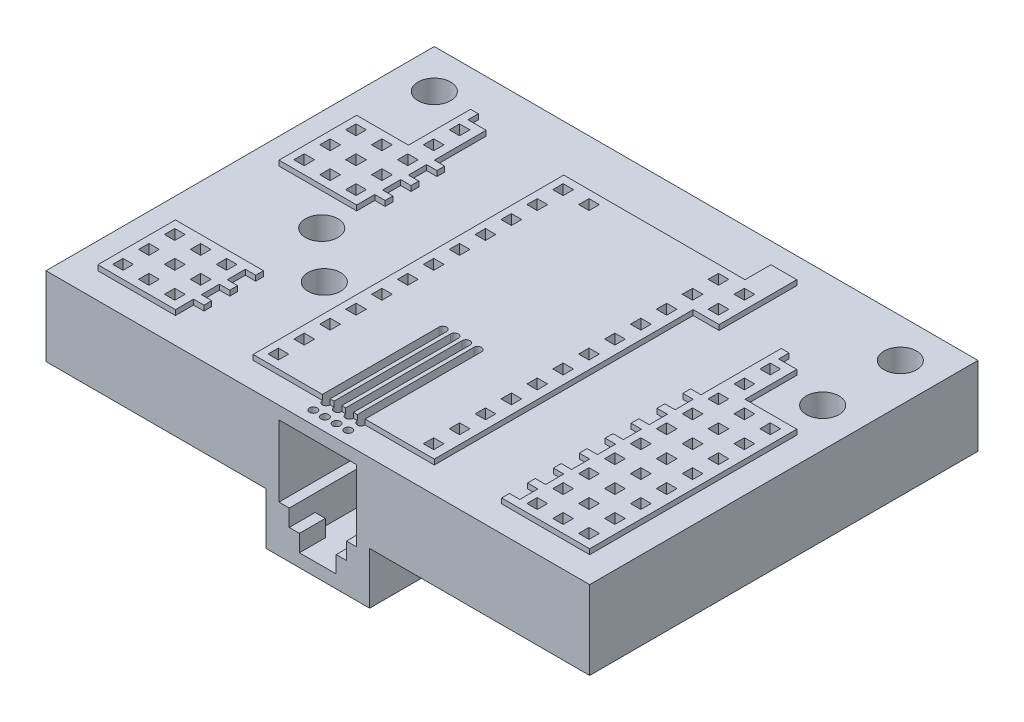
SolidWorks part; units mm, degrees
material "ABS PC"
ref_plane "Front Plane" through (0, 0, 0) normal (0, 0, 1) x (1, 0, 0)
ref_plane "Top Plane" through (0, 0, 0) normal (0, 1, 0) x (1, 0, 0)
ref_plane "Right Plane" through (0, 0, 0) normal (1, 0, 0) x (0, 0, -1)
sketch "Sketch1" plane through (0, 0, 0) normal (0, 1, 0) x (1, 0, 0)
  line L0 (26.67, 19.05) -> (-26.67, -19.05) construction
  line L1 (-26.67, -19.05) -> (26.67, -19.05)
  line L2 (-26.67, -19.05) -> (-26.67, 19.05)
  line L3 (-26.67, 19.05) -> (26.67, 19.05)
  line L4 (26.67, -19.05) -> (26.67, 19.05)
  circle A0 centre (-22.86, 15.24) radius 1.6
  circle A1 centre (22.86, 15.24) radius 1.6
  circle A2 centre (22.86, 7.62) radius 1.6
  circle A3 centre (-16.764, -1.905) radius 1.6
  circle A4 centre (-12.065, -6.35) radius 1.6
  dimension "D3" = 3.2
  dimension "D1" = 38.1
  dimension "D2" = 53.34
  dimension "D4" = 3.81
  dimension "D5" = 3.81
  dimension "D6" = 3.81
  dimension "D7" = 3.81
  dimension "D8" = 3.81
  dimension "D9" = 11.43
  dimension "D10" = 9.906
  dimension "D11" = 14.605
  dimension "D12" = 12.7
  dimension "D13" = 17.145
extrude "breadboard" add sketch "Sketch1" along normal blind 8.2296
sketch "Sketch7" plane through (0, 0, 0) normal (0, -1, 0) x (1, 0, 0)
  line L1 (6.35, 16.256) -> (19.05, 16.256)
  line L2 (6.35, 16.256) -> (6.35, 14.224)
  line L3 (6.35, 14.224) -> (19.05, 14.224)
  line L4 (19.05, 16.256) -> (19.05, 14.224)
  line L6 (-26.67, 19.05) -> (26.67, 19.05) construction
  dimension "D1" = 12.7
  dimension "D2" = 2.032
  dimension "D3" = 2.794
  dimension "D4" = 6.35
extrude "Cut-Extrude5" cut sketch "Sketch7" against normal blind 7.1628
pattern_linear "LPattern4" count 10 spacing 2.54 along (0, 0, -1) count 2 spacing 25.4 along (-1, 0, 0) skipping (3, 1), (4, 1), (5, 1), (6, 1) of "Cut-Extrude5"
sketch "Sketch8" plane through (0, 0, 0) normal (0, -1, 0) x (1, 0, 0)
  line L0 (-26.67, -19.05) -> (-26.67, 19.05) construction
  line L1 (-23.876, 16.51) -> (-21.844, 16.51)
  line L2 (-23.876, 16.51) -> (-23.876, 3.81)
  line L3 (-23.876, 3.81) -> (-21.844, 3.81)
  line L4 (-21.844, 16.51) -> (-21.844, 3.81)
  line L5 (-26.67, 19.05) -> (26.67, 19.05) construction
  dimension "D1" = 12.7
  dimension "D2" = 2.032
  dimension "D3" = 2.794
  dimension "D4" = 2.54
extrude "Cut-Extrude6" cut sketch "Sketch8" against normal blind 7.1628
pattern_linear "LPattern5" count 2 spacing 12.7 along (0, 0, 1) count 2 spacing 2.54 along (1, 0, 0) of "Cut-Extrude6"
sketch "Sketch9" plane through (0, 0, 0) normal (0, -1, 0) x (1, 0, 0)
  line L0 (26.67, 19.05) -> (26.67, -19.05) construction
  line L1 (21.9075, 16.51) -> (23.8125, 16.51)
  line L2 (21.9075, 16.51) -> (21.9075, -3.81)
  line L3 (21.9075, -3.81) -> (23.8125, -3.81)
  line L4 (23.8125, 16.51) -> (23.8125, -3.81)
  line L5 (-26.67, 19.05) -> (26.67, 19.05) construction
  dimension "D1" = 20.32
  dimension "D2" = 1.905
  dimension "D3" = 2.8575
  dimension "D4" = 2.54
extrude "Cut-Extrude7" cut sketch "Sketch9" against normal blind 7.1628
pattern_linear "LPattern6" count 1 spacing 12.7 along (0, 0, -1) count 2 spacing 2.54 along (-1, 0, 0) of "Cut-Extrude7"
sketch "Sketch10" plane through (0, 7.1628, 0) normal (0, -1, 0) x (1, 0, 0)
  line L0 (-23.876, 16.51) -> (-23.876, -8.89) construction
  line L1 (-23.4315, 15.748) -> (-22.4155, 15.748)
  line L2 (-23.4315, 15.748) -> (-23.4315, 14.732)
  line L3 (-23.4315, 14.732) -> (-22.4155, 14.732)
  line L4 (-22.4155, 15.748) -> (-22.4155, 14.732)
  line L5 (-21.844, 16.51) -> (-23.876, 16.51) construction
  dimension "D1" = 1.016
  dimension "D2" = 1.016
  dimension "D3" = 0.4445
  dimension "D4" = 0.762
extrude "Cut-Extrude8" cut sketch "Sketch10" against normal through all
pattern_linear "LPattern8" count 12 spacing 2.54 along (0, 0, -1) count 19 spacing 2.54 along (1, 0, 0) skipping (0, 3), (0, 4), (0, 5), (0, 7), (0, 8), (0, 9), (0, 10), (0, 11), (0, 13), (0, 14), (0, 15), (1, 3), (1, 4), (1, 5), (1, 7), (1, 8), (1, 9), (1, 10), (1, 11), (1, 13), (1, 14), (1, 15), (2, 3), (2, 4), (2, 5), (2, 7), (2, 8), (2, 9), (2, 10), (2, 11), (2, 13), (2, 14), (2, 15), (3, 0), (3, 1), (3, 2), (3, 3), (3, 4), (3, 5), (3, 7), (3, 8), (3, 9), (3, 10), (3, 11), (3, 13), (3, 14), (3, 15), (4, 0), (4, 1), (4, 2), (4, 3), (4, 4), (4, 5), (4, 7), (4, 8), (4, 9), (4, 10), (4, 11), (4, 13), (4, 14), (4, 15), (5, 0), (5, 1), (5, 2), (5, 3), (5, 4), (5, 5), (5, 7), (5, 8), (5, 9), (5, 10), (5, 11), (5, 13), (5, 14), (5, 15), (6, 0), (6, 1), (6, 2), (6, 3), (6, 4), (6, 5), (6, 7), (6, 8), (6, 9), (6, 10), (6, 11), (6, 13), (6, 14), (6, 15), (7, 3), (7, 4), (7, 5), (7, 7), (7, 8), (7, 9), (7, 10), (7, 11), (7, 13), (7, 14), (7, 15), (8, 3), (8, 4), (8, 5), (8, 7), (8, 8), (8, 9), (8, 10), (8, 11), (8, 13), (8, 14), (8, 15), (8, 17), (8, 18), (9, 3), (9, 4), (9, 5), (9, 7), (9, 8), (9, 9), (9, 10), (9, 11), (9, 13), (9, 14), (9, 15), (9, 17), (9, 18), (10, 0), (10, 1), (10, 3), (10, 4), (10, 5), (10, 7), (10, 8), (10, 9), (10, 10), (10, 11), (10, 14), (10, 15), (10, 16), (10, 17), (10, 18), (11, 0), (11, 1), (11, 3), (11, 4), (11, 5), (11, 8), (11, 9), (11, 10), (11, 11), (11, 14), (11, 15), (11, 16), (11, 17), (11, 18) of "Cut-Extrude8"
sketch "Sketch12" plane through (0, 0, 0) normal (0, -1, 0) x (1, 0, 0)
  line L0 (-26.67, -19.05) -> (-26.67, 19.05) construction
  line L1 (-19.05, -9.144) -> (-6.35, -9.144)
  line L2 (-19.05, -9.144) -> (-19.05, -11.176)
  line L3 (-19.05, -11.176) -> (-6.35, -11.176)
  line L4 (-6.35, -9.144) -> (-6.35, -11.176)
  line L5 (26.67, -19.05) -> (-26.67, -19.05) construction
  dimension "D1" = 12.7
  dimension "D2" = 2.032
  dimension "D3" = 7.62
  dimension "D4" = 7.874
extrude "Cut-Extrude9" cut sketch "Sketch12" against normal blind 7.1628
pattern_linear "LPattern9" count 2 spacing 2.54 along (0, 0, -1) of "Cut-Extrude9"
sketch "Sketch47" plane through (0, 0, 0) normal (0, -1, 0) x (1, 0, 0)
  line L0 (-26.67, 19.05) -> (26.67, 19.05) construction
  line L1 (5.08, 6.35) -> (-5.08, 6.35)
  line L2 (5.08, 6.35) -> (5.08, 19.05)
  line L3 (5.08, 19.05) -> (-5.08, 19.05)
  line L4 (-5.08, 6.35) -> (-5.08, 19.05)
  line L5 (26.67, 19.05) -> (26.67, -19.05) construction
  dimension "D1" = 10.16
  dimension "D2" = 12.7
  dimension "D3" = 21.59
extrude "Boss-Extrude5" add sketch "Sketch47" along normal blind 5.08
sketch "Sketch54" plane through (0, 0, 19.05) normal (0, 0, 1) x (1, 0, 0)
  line L1 (-3.81, 6.477) -> (3.81, 6.477)
  line L2 (-3.81, 6.477) -> (-3.81, -0.508)
  line L3 (-1.8034, -3.81) -> (1.8034, -3.81)
  line L4 (3.81, 6.477) -> (3.81, -0.508)
  line L5 (26.67, 8.2296) -> (26.67, 0) construction
  line L7 (-3.81, -0.508) -> (-2.8067, -0.508)
  line L8 (-2.8067, -0.508) -> (-2.8067, -2.159)
  line L9 (-2.8067, -2.159) -> (-1.8034, -2.159)
  line L10 (-1.8034, -2.159) -> (-1.8034, -3.81)
  line L12 (1.8034, -3.81) -> (1.8034, -2.159)
  line L13 (1.8034, -2.159) -> (2.8067, -2.159)
  line L14 (2.8067, -2.159) -> (2.8067, -0.508)
  line L15 (2.8067, -0.508) -> (3.81, -0.508)
  dimension "D1" = 7.62
  dimension "D2" = 22.86
  dimension "D3" = 6.985
  dimension "D5" = 5.6134
  dimension "D6" = 1.0033
  dimension "D7" = 3.6068
  dimension "D8" = 1.0033
  dimension "D9" = 1.651
  dimension "D10" = 1.651
  dimension "D11" = 1.651
  dimension "D12" = 1.651
extrude "Cut-Extrude33" cut sketch "Sketch54" against normal blind 10.9982
sketch "Sketch57" plane through (0, -2.159, 0) normal (0, 1, 0) x (1, 0, 0)
  line L0 (-2.8067, -8.0518) -> (-2.8067, -19.05) construction
  line L1 (2.8067, -6.7818) -> (-2.8067, -6.7818)
  line L2 (2.8067, -6.7818) -> (2.8067, -16.51)
  line L3 (2.8067, -16.51) -> (-2.8067, -16.51)
  line L4 (-2.8067, -6.7818) -> (-2.8067, -16.51)
  dimension "D2" = 9.7282
  dimension "D3" = 5.6134
extrude "Cut-Extrude34" cut sketch "Sketch57" against normal blind 1.651
sketch "Sketch59" plane through (0, 0, 8.0518) normal (0, 0, 1) x (1, 0, 0)
  line L0 (3.81, 6.477) -> (-3.81, 6.477) construction
  line L1 (-2.0955, 6.477) -> (-1.3335, 6.477)
  line L2 (-2.0955, 6.477) -> (-2.0955, 2.413)
  line L3 (-2.0955, 2.413) -> (-1.3335, 2.413)
  line L4 (-1.3335, 6.477) -> (-1.3335, 2.413)
  line L6 (0, -3.81) -> (0, 9.3002) construction
  line L7 (-2.8067, -3.81) -> (2.8067, -3.81) construction
  line L8 (-1.7145, 2.413) -> (-1.7145, 8.2296) construction
  line L9 (-26.67, 8.2296) -> (26.67, 8.2296) construction
  dimension "D1" = 4.064
  dimension "D2" = 0.762
  dimension "D3" = 1.7145
extrude "Cut-Extrude35" cut sketch "Sketch59" against normal blind 5.08
pattern_linear "LPattern25" count 4 spacing 1.143 along (1, 0, 0) of "Cut-Extrude35"
sketch "Sketch62" plane through (0, 8.2296, 0) normal (0, 1, 0) x (1, 0, 0)
  line L1 (-26.67, -19.05) -> (26.67, -19.05) construction
  line L2 (-26.67, 19.05) -> (-26.67, -19.05) construction
  circle A0 centre (-1.7145, -5.08) radius 0.381
  dimension "D1" = 0.762
  dimension "D2" = 24.9555
  dimension "D3" = 13.97
extrude "Cut-Extrude37" cut sketch "Sketch62" against normal blind 7.62
pattern_linear "LPattern27" count 4 spacing 1.143 along (1, 0, 0) count 2 spacing 12.7 along (0, 0, 1) of "Cut-Extrude37"
sketch "Sketch63" plane through (0, 8.2296, 0) normal (0, 1, 0) x (1, 0, 0)
  line L0 (-1.7145, -16.51) -> (-1.7145, -5.08) construction
  line L1 (-2.0955, -16.51) -> (-2.0955, -5.08)
  line L2 (-1.3335, -16.51) -> (-1.3335, -5.08)
  arc A0 (-2.0955, -16.51) -> (-1.3335, -16.51) centre (-1.7145, -16.51) ccw
  arc A1 (-1.3335, -5.08) -> (-2.0955, -5.08) centre (-1.7145, -5.08) ccw
  point P4 (-1.7145, -10.795)
  dimension "D1" = 0.381
extrude "Cut-Extrude38" cut sketch "Sketch63" against normal blind 1.27
pattern_linear "LPattern28" count 4 spacing 1.143 along (1, 0, 0) of "Cut-Extrude38"
sketch "Sketch66" plane through (0, 0, 8.0518) normal (0, 0, 1) x (1, 0, 0)
  line L0 (-2.8067, -0.508) -> (-2.8067, -2.159) construction
  line L1 (-2.8067, -2.2225) -> (2.8067, -2.2225)
  line L2 (-2.8067, -2.2225) -> (-2.8067, 0.9525)
  line L3 (-2.8067, 0.9525) -> (2.8067, 0.9525)
  line L4 (2.8067, -2.2225) -> (2.8067, 0.9525)
  line L6 (-2.8067, -3.81) -> (2.8067, -3.81) construction
  dimension "D1" = 5.6134
  dimension "D2" = 3.175
  dimension "D3" = 1.5875
extrude "Cut-Extrude41" cut sketch "Sketch66" against normal blind 0.508
sketch "Sketch68" plane through (0, 0, 0) normal (0, -1, 0) x (1, 0, 0)
  line L0 (-6.35, -13.716) -> (-6.35, -11.684) construction
  line L1 (-6.0325, -11.684) -> (-0.9525, -11.684)
  line L2 (-6.0325, -11.684) -> (-6.0325, -13.716)
  line L3 (-6.0325, -13.716) -> (-0.9525, -13.716)
  line L4 (-0.9525, -11.684) -> (-0.9525, -13.716)
  line L6 (-6.35, -11.684) -> (-19.05, -11.684) construction
  dimension "D1" = 5.08
  dimension "D2" = 2.032
  dimension "D3" = 0.3175
extrude "Cut-Extrude43" cut sketch "Sketch68" against normal blind 7.1628
sketch "Sketch69" plane through (0, 0, 0) normal (0, -1, 0) x (1, 0, 0)
  line L0 (-19.05, -13.97) -> (-19.05, -8.89)
  line L1 (23.8125, -3.81) -> (23.8125, -5.5419)
  line L2 (19.05, -3.81) -> (23.8125, -3.81)
  line L3 (-19.05, -8.89) -> (-23.876, -8.89)
  line L4 (3.175, 6.096) -> (3.175, -13.97)
  line L5 (3.175, 6.096) -> (-6.35, 6.096)
  line L6 (19.05, 6.096) -> (6.35, 6.096) construction
  line L7 (-6.35, 6.096) -> (-6.35, 4.064)
  line L8 (-23.876, -8.89) -> (-23.876, -13.1922)
  line L9 (-20.9592, -16.51) -> (20.9592, -16.51)
  line L11 (23.8125, -9.6981) -> (23.8125, -13.1619)
  line L12 (-6.35, 4.064) -> (-3.175, 4.064)
  line L13 (-19.05, -13.97) -> (-3.175, -13.97)
  line L15 (19.05, -3.81) -> (19.05, -8.636)
  line L16 (-3.175, -13.97) -> (-3.175, 4.064)
  line L17 (6.35, -8.636) -> (19.05, -8.636) construction
  line L18 (19.05, -8.636) -> (19.05, -6.604) construction
  line L19 (3.175, -13.97) -> (11.43, -13.97)
  line L20 (11.43, -13.97) -> (11.43, -8.636)
  line L21 (6.35, 4.064) -> (19.05, 4.064) construction
  line L22 (11.43, -8.636) -> (19.05, -8.636)
  line L23 (6.35, -6.604) -> (6.35, -8.636) construction
  line L24 (-19.05, -6.604) -> (-19.05, -8.636) construction
  line L25 (0, 0) -> (0, -30.7644) construction
  line L26 (-6.35, 9.144) -> (-6.35, 11.176) construction
  line L31 (26.67, -19.05) -> (-26.67, -19.05) construction
  arc A0 (23.8125, -5.5419) -> (23.8125, -9.6981) centre (22.86, -7.62) ccw
  arc A1 (23.8125, -13.1619) -> (20.9592, -16.51) centre (22.86, -15.24) ccw
  arc A2 (-20.9592, -16.51) -> (-23.876, -13.1922) centre (-22.86, -15.24) ccw
  dimension "D6" = 3.175
  dimension "D1" = 4.572
  dimension "D2" = 2.54
  dimension "D3" = 2.54
  dimension "D4" = 5.08
  dimension "D7" = 3.175
extrude "tracing" cut sketch "Sketch69" against normal blind 1.5748
sketch "Sketch80" plane through (0, 0, 0) normal (0, -1, 0) x (1, 0, 0)
  line L0 (-6.35, 4.064) -> (-3.175, 4.064) construction
  line L1 (-3.81, 6.096) -> (-8.89, 6.096)
  line L2 (-3.81, 6.096) -> (-3.81, 4.064)
  line L3 (-3.81, 4.064) -> (-8.89, 4.064)
  line L4 (-8.89, 6.096) -> (-8.89, 4.064)
  line L5 (-6.35, -3.556) -> (-6.35, -1.524) construction
  line L6 (19.05, 6.096) -> (6.35, 6.096) construction
  line L8 (6.35, 4.064) -> (19.05, 4.064) construction
  dimension "D1" = 5.08
  dimension "D2" = 2.54
extrude "Cut-Extrude52" cut sketch "Sketch80" against normal blind 7.1628
sketch "Sketch77" plane through (0, 0, 0) normal (0, -1, 0) x (1, 0, 0)
  line L0 (-21.844, -8.89) -> (-21.844, 16.51) construction
  line L1 (-23.876, 16.51) -> (-21.844, 16.51)
  line L2 (-23.876, 16.51) -> (-23.876, 17.78)
  line L3 (-23.876, 17.78) -> (-21.844, 17.78)
  line L4 (-21.844, 16.51) -> (-21.844, 17.78)
  dimension "D1" = 1.27
extrude "Cut-Extrude51" cut sketch "Sketch77" against normal blind 1.5748
pattern_linear "LPattern32" count 2 spacing 2.54 along (1, 0, 0) count 2 spacing 26.67 of "Cut-Extrude51"
sketch "Sketch81" plane through (0, 0, 0) normal (0, -1, 0) x (1, 0, 0)
  line L0 (21.2725, -3.81) -> (21.2725, 16.51) construction
  line L1 (19.3675, 16.51) -> (21.2725, 16.51)
  line L2 (19.3675, 16.51) -> (19.3675, 17.78)
  line L3 (19.3675, 17.78) -> (21.2725, 17.78)
  line L4 (21.2725, 16.51) -> (21.2725, 17.78)
  dimension "D1" = 1.27
extrude "Cut-Extrude53" cut sketch "Sketch81" against normal blind 1.5748
pattern_linear "LPattern33" count 2 spacing 2.54 along (1, 0, 0) count 2 spacing 21.59 of "Cut-Extrude53"
sketch "Sketch85" plane through (0, 0, 0) normal (0, -1, 0) x (1, 0, 0)
  line L1 (-8.6995, 1.016) -> (-6.6675, 1.016)
  line L2 (-8.6995, 1.016) -> (-8.6995, -1.016)
  line L3 (-8.6995, -1.016) -> (-6.6675, -1.016)
  line L4 (-6.6675, 1.016) -> (-6.6675, -1.016)
  line L8 (-8.1915, 4.572) -> (-7.1755, 4.572) construction
  line L9 (-7.1755, 4.572) -> (-7.1755, 5.588) construction
  dimension "D1" = 5.588
  dimension "D2" = 2.032
  dimension "D3" = 2.032
  dimension "D4" = 0.508
extrude "Cut-Extrude57" cut sketch "Sketch85" against normal blind 7.1628
pattern_linear "LPattern34" count 4 spacing 2.54 along (0, 0, 1) skipping (2, 0) of "Cut-Extrude57"
sketch "Sketch86" plane through (0, 0, 0) normal (0, -1, 0) x (1, 0, 0)
  line L0 (-5.08, 19.05) -> (-5.08, 6.35) construction
  line L1 (-6.35, 16.256) -> (-5.08, 16.256)
  line L2 (-6.35, 16.256) -> (-6.35, 14.224)
  line L3 (-6.35, 14.224) -> (-5.08, 14.224)
  line L4 (-5.08, 16.256) -> (-5.08, 14.224)
  line L5 (-19.05, 14.224) -> (-6.35, 14.224) construction
extrude "Cut-Extrude58" cut sketch "Sketch86" against normal blind 1.5748
pattern_linear "LPattern35" count 12 spacing 2.54 along (0, 0, -1) count 2 spacing 11.43 along (1, 0, 0) skipping (3, 0), (4, 0), (5, 0), (6, 0), (11, 0) of "Cut-Extrude58"
sketch "Sketch88" plane through (0, 0, 0) normal (0, -1, 0) x (1, 0, 0)
  line L0 (-6.35, -9.144) -> (-19.05, -9.144) construction
  line L1 (6.35, -9.144) -> (11.43, -9.144)
  line L2 (6.35, -9.144) -> (6.35, -11.176)
  line L3 (6.35, -11.176) -> (11.43, -11.176)
  line L4 (11.43, -9.144) -> (11.43, -11.176)
  line L6 (6.35, -6.604) -> (6.35, -8.636) construction
  dimension "D1" = 5.08
extrude "Cut-Extrude59" cut sketch "Sketch88" against normal blind 7.1628
pattern_linear "LPattern36" count 2 spacing 2.54 along (0, 0, -1) of "Cut-Extrude59"
sketch "Sketch89" plane through (0, 8.2296, 0) normal (0, 1, 0) x (1, 0, 0)
  line L0 (-24.13, -8.89) -> (-15.494, -8.89)
  line L1 (-26.67, 19.05) -> (26.67, 19.05)
  line L2 (-26.67, 19.05) -> (-26.67, -19.05)
  line L3 (-26.67, -19.05) -> (26.67, -19.05)
  line L4 (26.67, 19.05) -> (26.67, -19.05)
  line L5 (-16.51, -16.51) -> (-24.13, -16.51)
  line L6 (-16.51, -16.51) -> (-16.51, -14.732)
  line L7 (-16.51, -11.43) -> (-16.51, -9.652)
  line L8 (-24.13, -16.51) -> (-24.13, -8.89)
  line L9 (-16.51, -11.43) -> (-15.494, -11.43)
  line L10 (-16.51, -13.97) -> (-16.51, -12.192)
  line L11 (-16.51, -9.652) -> (-15.494, -9.652)
  line L12 (-15.494, -8.89) -> (-15.494, -9.652)
  line L13 (-16.51, -12.192) -> (-15.494, -12.192)
  line L14 (-15.494, -11.43) -> (-15.494, -12.192)
  line L15 (-16.51, -13.97) -> (-15.494, -13.97)
  line L16 (-16.51, 8.89) -> (-16.51, 13.97)
  line L17 (-16.51, -14.732) -> (-15.494, -14.732)
  line L18 (-15.494, -13.97) -> (-15.494, -14.732)
  line L19 (-24.13, 1.27) -> (-16.51, 1.27)
  line L20 (-24.13, 1.27) -> (-24.13, 8.89)
  line L21 (-18.288, 13.97) -> (-16.51, 13.97)
  line L22 (-16.51, 1.27) -> (-16.51, 3.048)
  line L23 (-16.51, 6.35) -> (-16.51, 8.128)
  line L24 (-16.51, 3.81) -> (-16.51, 5.588)
  line L25 (-24.13, 8.89) -> (-19.05, 8.89)
  line L26 (-19.05, 14.986) -> (-19.05, 8.89)
  line L27 (-19.05, 13.97) -> (-3.175, 13.97) construction
  line L28 (-8.89, 13.97) -> (8.89, 13.97)
  line L29 (-19.05, 14.986) -> (-18.288, 14.986)
  line L30 (-18.288, 13.97) -> (-18.288, 14.986)
  line L31 (-16.51, 8.128) -> (-15.494, 8.128)
  line L32 (-8.89, 13.97) -> (-8.89, -16.51)
  line L33 (-16.51, 8.89) -> (-15.494, 8.89)
  line L34 (-15.494, 8.128) -> (-15.494, 8.89)
  line L35 (-16.51, 6.35) -> (-15.494, 6.35)
  line L36 (-8.89, -16.51) -> (8.89, -16.51)
  line L37 (-16.51, 5.588) -> (-15.494, 5.588)
  line L38 (-15.494, 6.35) -> (-15.494, 5.588)
  line L39 (-16.51, 3.81) -> (-15.494, 3.81)
  line L40 (8.89, 8.89) -> (8.89, -16.51)
  line L41 (-16.51, 3.048) -> (-15.494, 3.048)
  line L42 (-15.494, 3.81) -> (-15.494, 3.048)
  line L43 (-20.9592, 16.51) -> (20.9592, 16.51) construction
  line L44 (8.89, 16.51) -> (11.43, 16.51)
  line L45 (8.89, 16.51) -> (8.89, 13.97)
  line L46 (8.89, 8.89) -> (11.43, 8.89)
  line L47 (11.43, 16.51) -> (11.43, 8.89)
  line L48 (0, 0) -> (0, 30.7644) construction
  line L50 (17.272, 8.89) -> (19.05, 8.89)
  line L51 (16.51, 2.032) -> (16.51, 9.906)
  line L52 (15.494, -16.51) -> (24.13, -16.51)
  line L53 (24.13, 3.81) -> (24.13, -16.51)
  line L54 (16.51, 1.27) -> (16.51, -0.508)
  line L55 (16.51, -1.27) -> (16.51, -3.048)
  line L56 (16.51, -3.81) -> (16.51, -5.588)
  line L57 (24.13, 3.81) -> (19.05, 3.81)
  line L58 (19.05, 8.89) -> (19.05, 3.81)
  line L59 (16.51, -6.35) -> (16.51, -8.128)
  line L61 (16.51, 9.906) -> (17.272, 9.906)
  line L62 (17.272, 8.89) -> (17.272, 9.906)
  line L64 (16.51, -11.43) -> (16.51, -13.208)
  line L65 (16.51, -15.748) -> (15.494, -15.748)
  line L66 (15.494, -16.51) -> (15.494, -15.748)
  line L67 (16.51, -13.97) -> (15.494, -13.97)
  line L69 (16.51, -13.208) -> (15.494, -13.208)
  line L70 (15.494, -13.97) -> (15.494, -13.208)
  line L71 (16.51, -11.43) -> (15.494, -11.43)
  line L73 (16.51, -10.668) -> (15.494, -10.668)
  line L74 (15.494, -11.43) -> (15.494, -10.668)
  line L75 (16.51, -8.89) -> (15.494, -8.89)
  line L76 (16.51, -13.97) -> (16.51, -15.748)
  line L77 (16.51, -8.128) -> (15.494, -8.128)
  line L78 (15.494, -8.89) -> (15.494, -8.128)
  line L79 (16.51, -6.35) -> (15.494, -6.35)
  line L80 (16.51, -8.89) -> (16.51, -10.668)
  line L81 (16.51, -5.588) -> (15.494, -5.588)
  line L82 (15.494, -6.35) -> (15.494, -5.588)
  line L83 (16.51, -3.81) -> (15.494, -3.81)
  line L85 (16.51, -3.048) -> (15.494, -3.048)
  line L86 (15.494, -3.81) -> (15.494, -3.048)
  line L87 (16.51, -1.27) -> (15.494, -1.27)
  line L89 (16.51, -0.508) -> (15.494, -0.508)
  line L90 (15.494, -1.27) -> (15.494, -0.508)
  line L91 (16.51, 1.27) -> (15.494, 1.27)
  line L93 (16.51, 2.032) -> (15.494, 2.032)
  line L94 (15.494, 1.27) -> (15.494, 2.032)
  dimension "D1" = 7.62
  dimension "D2" = 7.62
  dimension "D3" = 2.54
  dimension "D4" = 2.54
  dimension "D5" = 1.016
  dimension "D6" = 0.762
  dimension "D7" = 0.762
  dimension "D8" = 0.762
  dimension "D9" = 1.778
  dimension "D10" = 1.778
  dimension "D11" = 10.16
  dimension "D12" = 7.62
  dimension "D13" = 5.08
  dimension "D14" = 1.016
  dimension "D15" = 0.762
  dimension "D16" = 2.54
  dimension "D17" = 0.762
  dimension "D18" = 0.762
  dimension "D19" = 0.762
  dimension "D20" = 1.778
  dimension "D21" = 1.778
  dimension "D22" = 1.778
  dimension "D23" = 8.89
  dimension "D24" = 8.89
  dimension "D25" = 2.54
  dimension "D26" = 2.54
  dimension "D27" = 2.54
  dimension "D28" = 0.762
  dimension "D29" = 1.016
  dimension "D30" = 1.778
  dimension "D31" = 0.762
  dimension "D32" = 1.016
  dimension "D33" = 5.08
  dimension "D34" = 7.62
extrude "Cut-Extrude60" cut sketch "Sketch89" against normal blind 0.508
